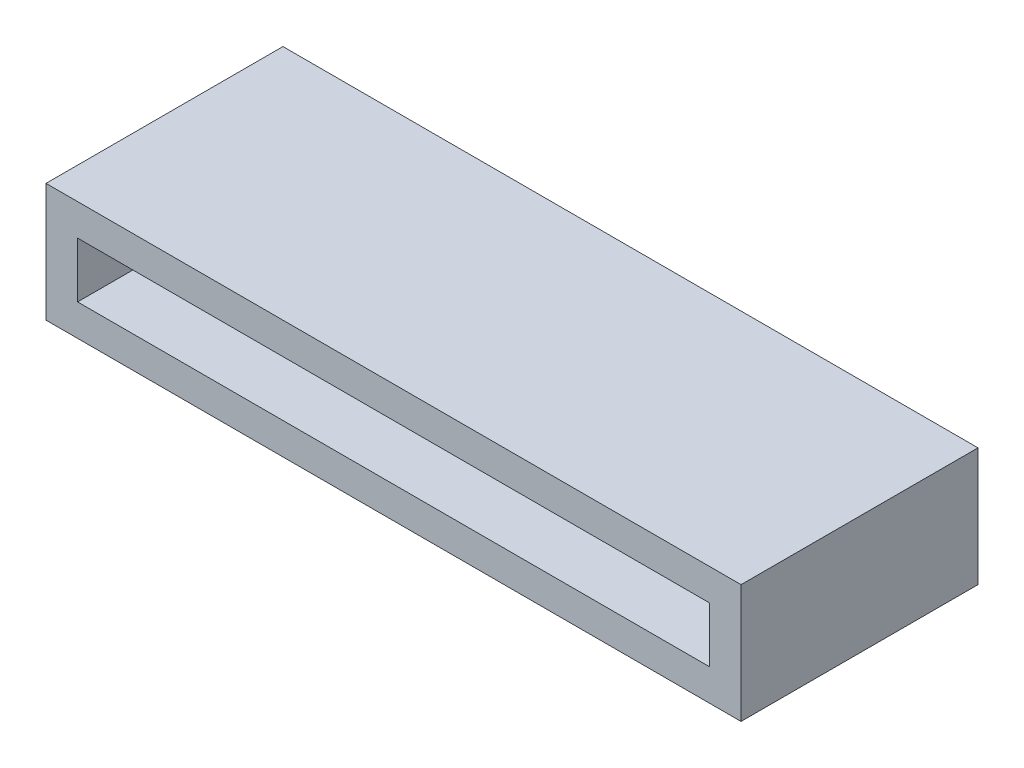
SolidWorks part; units mm, degrees
ref_plane "Front Plane" through (0, 0, 0) normal (0, 0, 1) x (1, 0, 0)
ref_plane "Top Plane" through (0, 0, 0) normal (0, 1, 0) x (1, 0, 0)
ref_plane "Right Plane" through (0, 0, 0) normal (1, 0, 0) x (0, 0, -1)
sketch "Sketch1" plane through (0, 0, 0) normal (0, 0, 1) x (1, 0, 0)
  line L1 (11, 1.875) -> (-11, 1.875)
  line L2 (11, 1.875) -> (11, -1.875)
  line L3 (11, -1.875) -> (-11, -1.875)
  line L4 (-11, 1.875) -> (-11, -1.875)
  line L5 (11, 1.875) -> (-11, -1.875) construction
  line L6 (11, -1.875) -> (-11, 1.875) construction
  point P0 (0, 0)
  dimension "D1" = 22
  dimension "D2" = 3.75
extrude "Boss-Extrude1" add sketch "Sketch1" along normal blind 7.5
shell "Shell1" thickness 1
